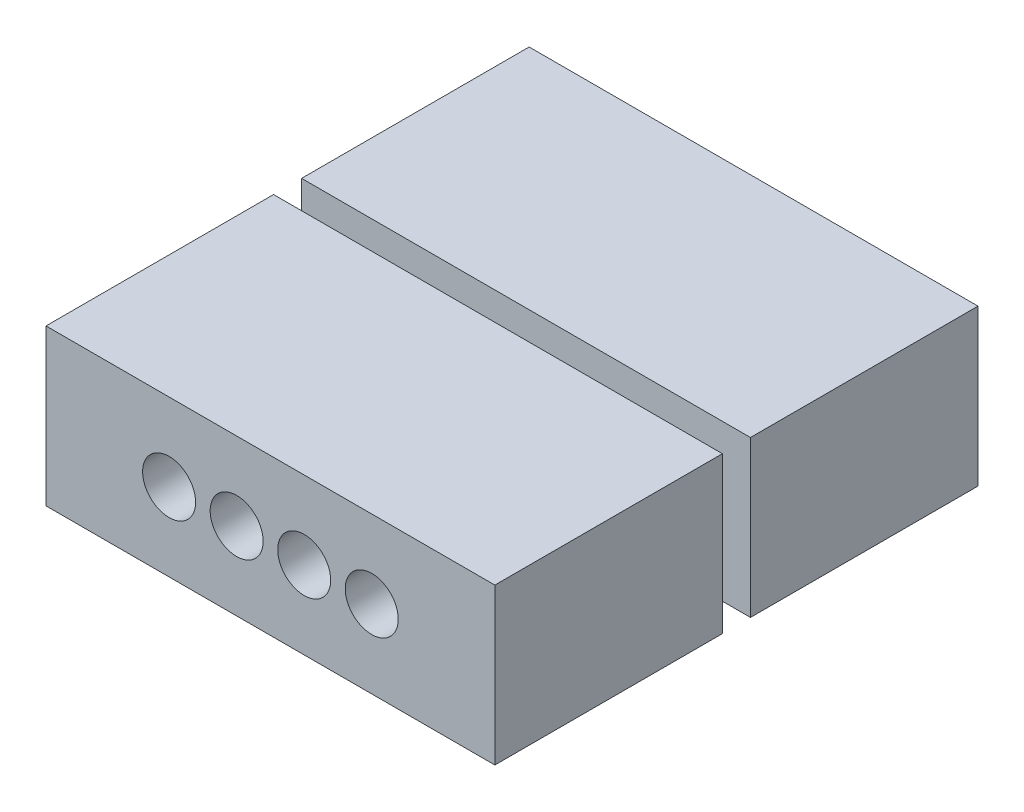
SolidWorks part; units mm, degrees
material "acero"
ref_plane "Alzado" through (0, 0, 0) normal (0, 0, 1) x (1, 0, 0)
ref_plane "Planta" through (0, 0, 0) normal (0, 1, 0) x (1, 0, 0)
ref_plane "Vista lateral" through (0, 0, 0) normal (1, 0, 0) x (0, 0, -1)
sketch "Sketch1" plane through (0, 0, 0) normal (0, 1, 0) x (1, 0, 0)
  line L1 (-7.2, -7.75) -> (7.2, -7.75)
  line L2 (-7.2, -7.75) -> (-7.2, -0.45)
  line L3 (-7.2, 7.75) -> (7.2, 7.75)
  line L4 (7.2, -7.75) -> (7.2, -0.45)
  line L5 (-7.2, -7.75) -> (7.2, 7.75) construction
  line L6 (-7.2, 7.75) -> (7.2, -7.75) construction
  line L8 (7.2, 0.45) -> (7.2, 7.75)
  line L9 (-7.2, 0.45) -> (-6.2, 0.45)
  line L11 (-7.2, -0.45) -> (-6.2, -0.45)
  line L12 (-6.2, 0.45) -> (-6.2, -0.45)
  line L13 (7.2, 0.45) -> (6.2, 0.45)
  line L14 (-7.2, 0.45) -> (-7.2, 7.75)
  line L15 (7.2, -0.45) -> (6.2, -0.45)
  line L16 (6.2, 0.45) -> (6.2, -0.45)
  point P0 (0, 0)
  dimension "D1" = 14.4
  dimension "D2" = 15.5
  dimension "D5" = 7.3
  dimension "D7" = 7.3
  dimension "D9" = 1
extrude "Boss-Extrude1" add sketch "Sketch1" along normal blind 5
sketch "Sketch2" plane through (0, 5, 0) normal (0, 1, 0) x (1, 0, 0)
  line L1 (-7.2, 0.45) -> (-6.2, 0.45) construction
  line L2 (-6.2, -0.45) -> (-7.2, -0.45) construction
  line L5 (-6.2, 0.45) -> (-6.2, -0.45) construction
  line L6 (-6.2, -0.45) -> (6.2, -0.45)
  line L7 (-6.2, -0.45) -> (-6.2, 0.45)
  line L8 (-6.2, 0.45) -> (6.2, 0.45)
  line L9 (6.2, -0.45) -> (6.2, 0.45)
  line L10 (6.2, -0.45) -> (6.2, 0.45) construction
extrude "Cut-Extrude1" cut sketch "Sketch2" against normal blind 1.5
sketch "Croquis1" plane through (0, 0, 7.75) normal (0, 0, 1) x (1, 0, 0)
  line L0 (-3.25, 2.5) -> (-1.0833, 2.5) construction
  line L1 (-1.0833, 2.5) -> (1.0833, 2.5) construction
  line L2 (1.0833, 2.5) -> (3.25, 2.5) construction
  line L3 (0, 5) -> (0, 0) construction
  line L4 (-7.2, 5) -> (7.2, 5) construction
  circle A0 centre (-3.25, 2.5) radius 0.85
  circle A1 centre (-1.0833, 2.5) radius 0.85
  circle A2 centre (1.0833, 2.5) radius 0.85
  circle A3 centre (3.25, 2.5) radius 0.85
  point P13 (0, 2.5)
  dimension "D1" = 1.7
  dimension "D2" = 8.2
extrude "Cortar-Extruir1" cut sketch "Croquis1" against normal blind 3
sketch "Croquis2" plane through (0, 0, -7.75) normal (0, 0, -1) x (-1, 0, 0)
  line L0 (0, 0) -> (0, 2) construction
  line L1 (-4.7, 3.2) -> (4.7, 3.2)
  line L2 (-4.7, 3.2) -> (-4.7, 2)
  line L3 (-4.7, 2) -> (4.7, 2)
  line L4 (4.7, 3.2) -> (4.7, 2)
  line L5 (-7.2, 0) -> (7.2, 0) construction
  line L6 (-7.2, 5) -> (7.2, 5) construction
  dimension "D1" = 2
  dimension "D2" = 1.8
  dimension "D3" = 9.4
extrude "Cortar-Extruir2" cut sketch "Croquis2" against normal blind 7.5 contours L1 L4 L3 L2
